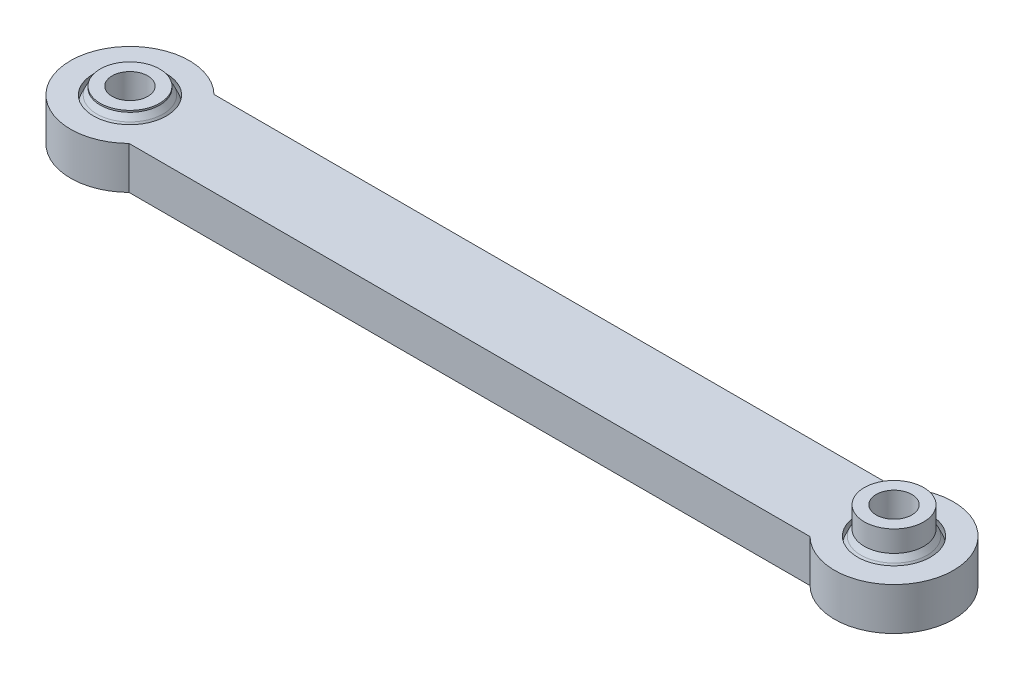
SolidWorks part; units mm, degrees
ref_plane "Front Plane" through (0, 0, 0) normal (0, 0, 1) x (1, 0, 0)
ref_plane "Top Plane" through (0, 0, 0) normal (0, 1, 0) x (1, 0, 0)
ref_plane "Right Plane" through (0, 0, 0) normal (1, 0, 0) x (0, 0, -1)
sketch "Sketch1" plane through (0, 0, 0) normal (0, 0, 1) x (1, 0, 0)
  line L0 (45, 0) -> (0, 0) construction
  line L1 (0, 0) -> (0, -7.1591) construction
  line L2 (0, 0) -> (-45, 0) construction
  line L3 (-45, -2.5) -> (-45, 2.5)
  line L8 (-52, 2.5) -> (-52, -2.5)
  line L10 (-49.3, -2.5) -> (-52, -2.5)
  line L11 (-49.9739, 0) -> (-50, 0)
  line L12 (-49.3, 2.5) -> (-52, 2.5)
  line L13 (45, -2.5) -> (45, 2.5)
  line L14 (49.3, 2.5) -> (52, 2.5)
  line L15 (52, 2.5) -> (52, -2.5)
  line L16 (49.3, -2.5) -> (52, -2.5)
  arc A0 (-49.3, 2.5) -> (-49.3, -2.5) centre (-45, 0) ccw
  arc A2 (49.3, 2.5) -> (49.3, -2.5) centre (45, 0) cw
  point P10 (-45, 0)
  point P17 (-45, 2.5)
  dimension "D1" = 5
revolve "Revolve1" add sketch "Sketch1" angle 360 about L3
sketch "Sketch2" plane through (0, 0, 0) normal (0, 0, 1) x (1, 0, 0)
  line L0 (0, 0) -> (45, 0) construction
  line L1 (45, -2.5) -> (45, 2.5)
  line L2 (45, 0) -> (52, 0) construction
  line L3 (52, 2.5) -> (52, -2.5) construction
  line L4 (52, 2.5) -> (52, -2.5)
  line L5 (52, 2.5) -> (49.3, 2.5)
  line L6 (52, -2.5) -> (49.3, -2.5)
  arc A0 (49.3, 2.5) -> (49.3, -2.5) centre (45, 0) cw
  arc A1 (49.3, -2.5) -> (49.3, 2.5) centre (45, 0) ccw construction
  point P8 (45, 0)
revolve "Revolve2" add sketch "Sketch2" angle 360 about L1
sketch "Sketch4" plane through (0, 2.5, 0) normal (0, 1, 0) x (1, 0, 0)
  line L0 (-40.101, 5) -> (-40.101, 3.4641)
  line L1 (40.101, 5) -> (40.101, 3.4641)
  line L2 (-40.101, 5) -> (40.101, 5)
  line L3 (40.101, -5) -> (-40.101, -5)
  line L4 (40.101, -3.4641) -> (40.101, -5)
  line L5 (-40.101, -3.4641) -> (-40.101, -5)
  circle A0 centre (-45, 0) radius 7 construction
  circle A1 centre (45, 0) radius 7 construction
  arc A2 (-40.101, -3.4641) -> (-40.101, 3.4641) centre (-45, 0) ccw
  arc A3 (40.101, 3.4641) -> (40.101, -3.4641) centre (45, 0) ccw
  dimension "D3" = 12
  dimension "D4" = 12
  dimension "D1" = 10
  dimension "D2" = 10
extrude "Boss-Extrude1" add sketch "Sketch4" against normal blind 5
sketch "Sketch5" plane through (0, 0, 0) normal (0, 0, 1) x (1, 0, 0)
  line L0 (0, 2.5) -> (0, -2.5) construction
  line L1 (-40.101, 2.5) -> (40.101, 2.5) construction
  line L2 (-40.101, -2.5) -> (40.101, -2.5) construction
  line L3 (-45, 2.5) -> (-45, 3.7) construction
  line L4 (-45, -2.5) -> (-45, 3.7)
  line L5 (-45, -2.5) -> (-48.9, -2.5)
  line L8 (-40.7, 2.5) -> (-49.3, 2.5) construction
  line L11 (45, -2.5) -> (48.9, -2.5)
  line L13 (-48.1, 3.7) -> (-48.1, 5.7)
  line L14 (-48.1, 5.7) -> (-45, 5.7)
  line L15 (-45, 3.7) -> (-45, 5.7)
  line L16 (48.1, 3.7) -> (48.1, 5.7)
  line L17 (48.1, 5.7) -> (45, 5.7)
  line L18 (45, 3.7) -> (45, 5.7)
  line L19 (45, -2.5) -> (45, 3.7)
  arc A0 (-48.9, 2.5) -> (-49.5, 0) centre (-45.0063, 0.2435) ccw
  arc A3 (-48.9, -2.5) -> (-49.5, 0) centre (-45.0063, -0.2435) cw
  arc A4 (-48.9, 2.5) -> (-48.1, 3.7) centre (-66.8683, 15.3455) ccw
  arc A5 (48.9, -2.5) -> (49.5, 0) centre (45.0063, -0.2435) ccw
  arc A6 (48.9, 2.5) -> (49.5, 0) centre (45.0063, 0.2435) cw
  arc A7 (48.9, 2.5) -> (48.1, 3.7) centre (66.8683, 15.3455) cw
  dimension "D1" = 2
  dimension "D2" = 3.9
  dimension "D4" = 3.1
revolve "Revolve3" add sketch "Sketch5" angle 360 about L4
sketch "Sketch6" plane through (0, 0, 0) normal (0, 0, 1) x (1, 0, 0)
  line L0 (45, 5.7) -> (45, -2.5)
  line L1 (45, -2.5) -> (48.9, -2.5)
  line L2 (45, 5.7) -> (48.1, 5.7)
  line L3 (48.1, 5.7) -> (48.1, 3.7)
  arc A0 (49.5, 0) -> (48.9, -2.5) centre (45.0063, -0.2435) cw
  arc A1 (48.9, 2.5) -> (49.5, 0) centre (45.0063, 0.2435) cw
  arc A2 (48.1, 3.7) -> (48.9, 2.5) centre (66.8683, 15.3455) ccw
revolve "Revolve4" add sketch "Sketch6" angle 360 about L0
sketch "Sketch7" plane through (0, 5.7, 0) normal (0, 1, 0) x (1, 0, 0)
  circle A0 centre (-45, 0) radius 2.1
  circle A1 centre (45, 0) radius 2.1
  dimension "D1" = 4.2
  dimension "D2" = 4.2
extrude "Cut-Extrude1" cut sketch "Sketch7" against normal blind 11
sketch "Sketch8" plane through (0, 5.7, 0) normal (0, 1, 0) x (1, 0, 0)
  circle A0 centre (-45, 0) radius 3.5
  circle A1 centre (45, 0) radius 3.5
  circle A2 centre (-45, 0) radius 2.1
  circle A3 centre (45, 0) radius 2.1
  dimension "D1" = 7
  dimension "D2" = 7
extrude "Boss-Extrude2" add sketch "Sketch8" against normal blind 2.5
sketch "Sketch9" plane through (0, 5.7, 0) normal (0, 1, 0) x (1, 0, 0)
  circle A0 centre (-45, 0) radius 5.0538
extrude "Cut-Extrude2" cut sketch "Sketch9" against normal blind 2
sketch "Sketch10" plane through (0, 3.7, 0) normal (0, 1, 0) x (1, 0, 0)
  circle A0 centre (-45, 0) radius 7.8446
extrude "Cut-Extrude3" cut sketch "Sketch10" against normal blind 0.3
